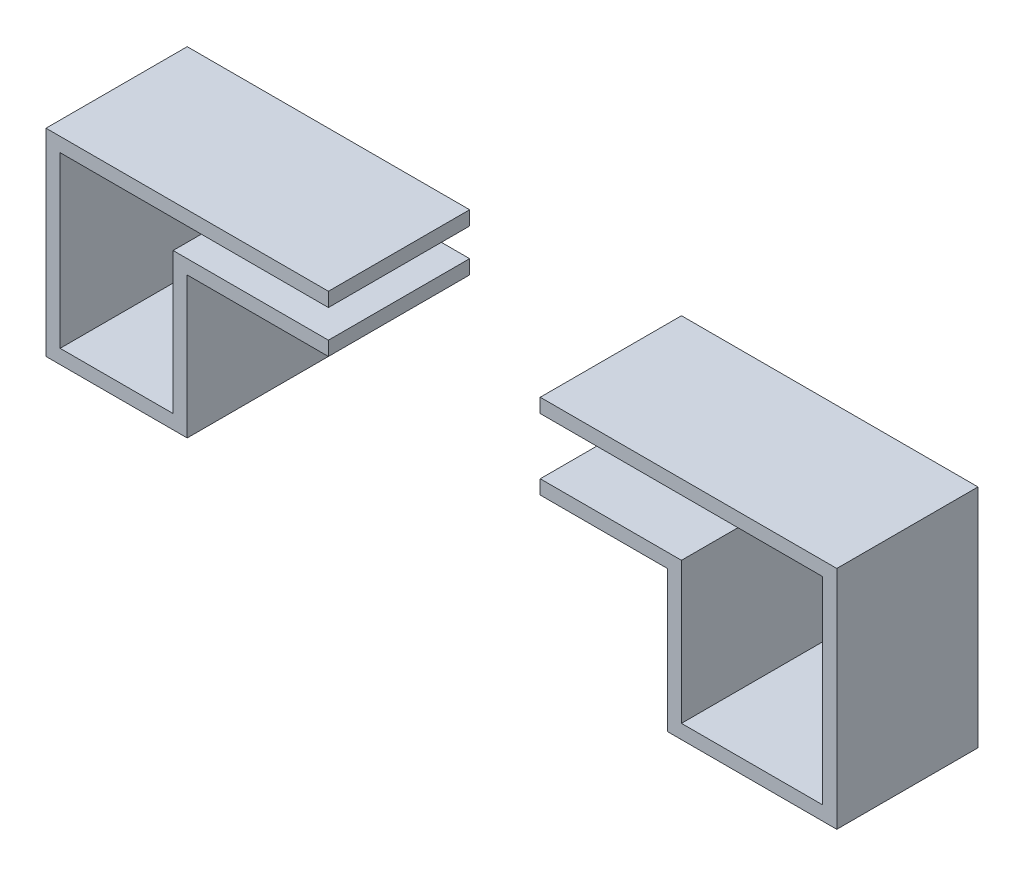
SolidWorks part; units mm, degrees
ref_plane "Front Plane" through (0, 0, 0) normal (0, 0, 1) x (1, 0, 0)
ref_plane "Top Plane" through (0, 0, 0) normal (0, 1, 0) x (1, 0, 0)
ref_plane "Right Plane" through (0, 0, 0) normal (1, 0, 0) x (0, 0, -1)
sketch "Sketch1" plane through (0, 0, 0) normal (0, 1, 0) x (1, 0, 0)
  line L0 (-0.875, 0) -> (0.875, 0)
  dimension "D1" = 1.75
sketch "Sketch2" plane through (0, 0, 0) normal (0, 0, 1) x (1, 0, 0)
  line L0 (-0.875, 0) -> (-0.875, 0.5)
  line L1 (-0.875, 0.5) -> (-0.375, 0.5)
  line L2 (0.875, 0) -> (0.875, 0.5)
  line L3 (0.875, 0.5) -> (0.375, 0.5)
  line L4 (1.375, 0) -> (1.375, 0.7)
  line L5 (1.375, 0.7) -> (0.375, 0.7)
  line L6 (-1.375, 0) -> (-1.375, 0.7)
  line L7 (-1.375, 0.7) -> (-0.375, 0.7)
  line L8 (-1.375, 0) -> (-0.875, 0)
  line L9 (0.875, 0) -> (1.375, 0)
  line L11 (-0.875, 0) -> (0.875, 0) construction
  point P15 (0, 0)
  point P17 (0, 0)
  point P19 (0, 0)
  point P20 (0, 0)
  dimension "D1" = 0.5
  dimension "D2" = 0.5
  dimension "D4" = 1
  dimension "D5" = 0.2
  dimension "D6" = 0.5
extrude "Extrude-Thin2" add sketch "Sketch2" along normal blind 0.5 thin thin type one direction wall 0.05
